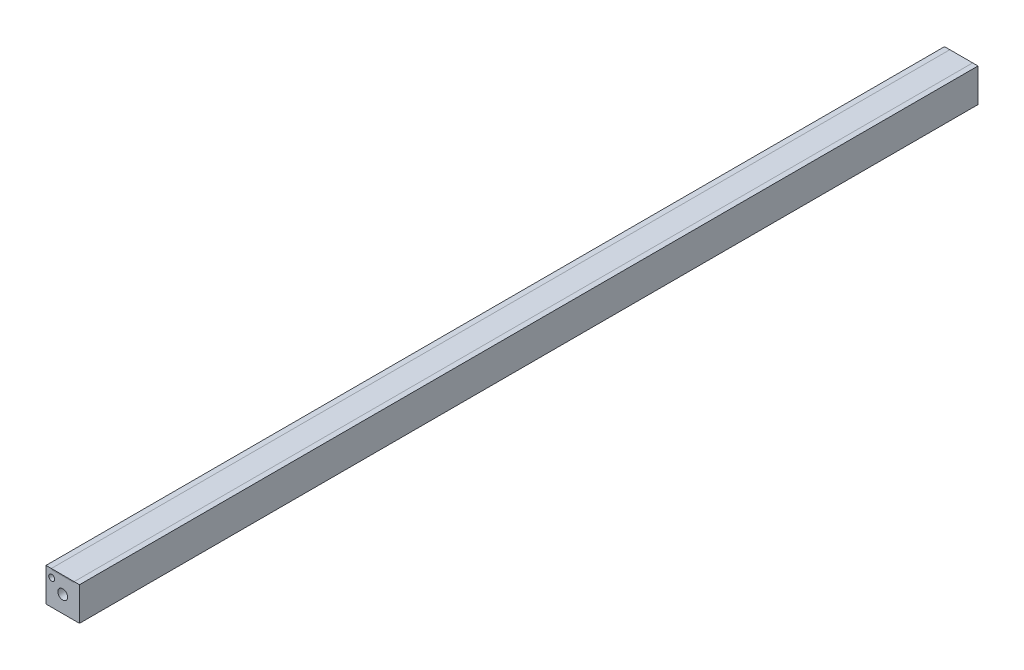
SolidWorks part; units mm, degrees
material "1060 Alloy"
ref_plane "Front Plane" through (0, 0, 0) normal (0, 0, 1) x (1, 0, 0)
ref_plane "Top Plane" through (0, 0, 0) normal (0, 1, 0) x (1, 0, 0)
ref_plane "Right Plane" through (0, 0, 0) normal (1, 0, 0) x (0, 0, -1)
sketch "Sketch1" plane through (0, 0, 0) normal (0, 0, 1) x (1, 0, 0)
  line L1 (0, 0) -> (18.63, 0)
  line L2 (0, 0) -> (0, -18.63)
  line L3 (0, -18.63) -> (18.63, -18.63)
  line L4 (18.63, 0) -> (18.63, -18.63)
  dimension "D1" = 18.63
extrude "Boss-Extrude1" add sketch "Sketch1" along normal blind 500
sketch "Sketch2" plane through (0, 0, 0) normal (0, 0, -1) x (-1, 0, 0)
  line L0 (-9.315, 0) -> (-9.315, -18.63) construction
  line L1 (-18.63, 0) -> (0, 0) construction
  line L2 (0, -18.63) -> (-18.63, -18.63) construction
  line L3 (-18.63, -9.315) -> (0, -9.315) construction
  line L4 (-18.63, -18.63) -> (-18.63, 0) construction
  line L5 (0, 0) -> (0, -18.63) construction
  circle A0 centre (-9.315, -9.315) radius 2.71
  dimension "D1" = 5.42
extrude "Cut-Extrude1" cut sketch "Sketch2" against normal blind 24
sketch "Sketch3" plane through (0, 0, 500) normal (0, 0, 1) x (1, 0, 0)
  circle A1 centre (9.315, -9.315) radius 2.71
  circle A2 centre (9.315, -9.315) radius 2.71
  dimension "D1" = 0
extrude "Cut-Extrude2" cut sketch "Sketch3" against normal blind 24
sketch "Sketch4" plane through (0, 0, 0) normal (0, 0, -1) x (-1, 0, 0)
  circle A0 centre (-14.95, -3.73) radius 1.67
  circle A1 centre (-14.95, -3.73) radius 1.585 construction
  dimension "D1" = 3.34
extrude "Cut-Extrude3" cut sketch "Sketch4" against normal blind 10
sketch "Sketch5" plane through (0, 0, 500) normal (0, 0, 1) x (1, 0, 0)
  line L0 (3.18, -4.345) -> (3.18, -18.63) construction
  line L1 (0, -18.63) -> (18.63, -18.63) construction
  line L2 (0, 0) -> (0, -18.63) construction
  circle A0 centre (3.18, -4.345) radius 1.67
  dimension "D1" = 3.34
  dimension "D2" = 3.18
  dimension "D3" = 14.285
extrude "Cut-Extrude4" cut sketch "Sketch5" against normal blind 10
sketch "Sketch6" plane through (0, 0, 0) normal (0, 1, 0) x (-1, 0, 0)
  line L1 (-15.665, 0) -> (-2.965, 0)
  line L2 (-15.665, 0) -> (-15.665, 500)
  line L3 (-15.665, 500) -> (-2.965, 500)
  line L4 (-2.965, 0) -> (-2.965, 500)
  line L5 (-18.63, 0) -> (0, 0) construction
  line L6 (-18.63, 500) -> (0, 500) construction
  line L7 (-9.315, 0) -> (-9.315, 500) construction
  line L9 (0, 500) -> (0, 0) construction
  line L10 (-18.63, 500) -> (-18.63, 0) construction
  dimension "D1" = 12.7
extrude "Cut-Extrude5" cut sketch "Sketch6" against normal blind 0.5
sketch "Sketch7" plane through (0, 0, 0) normal (0, 1, 0) x (-1, 0, 0)
  line L0 (-9.315, 500) -> (-9.315, 0) construction
  line L1 (-15.665, 0) -> (-2.965, 0)
  line L2 (-15.665, 0) -> (-15.665, 500)
  line L3 (-15.665, 500) -> (-2.965, 500)
  line L4 (-2.965, 0) -> (-2.965, 500)
  line L8 (-18.63, 0) -> (-15.665, 0) construction
  line L9 (-18.63, 500) -> (-15.665, 500) construction
  line L10 (-15.665, 500) -> (-15.665, 0) construction
  line L12 (-2.965, 0) -> (-2.965, 500) construction
  dimension "D1" = 12.7
extrude "Boss-Extrude2" add sketch "Sketch7" against normal up to surface (0.5 mm away) separate body up to face at (9.315, -0.5, 250)
